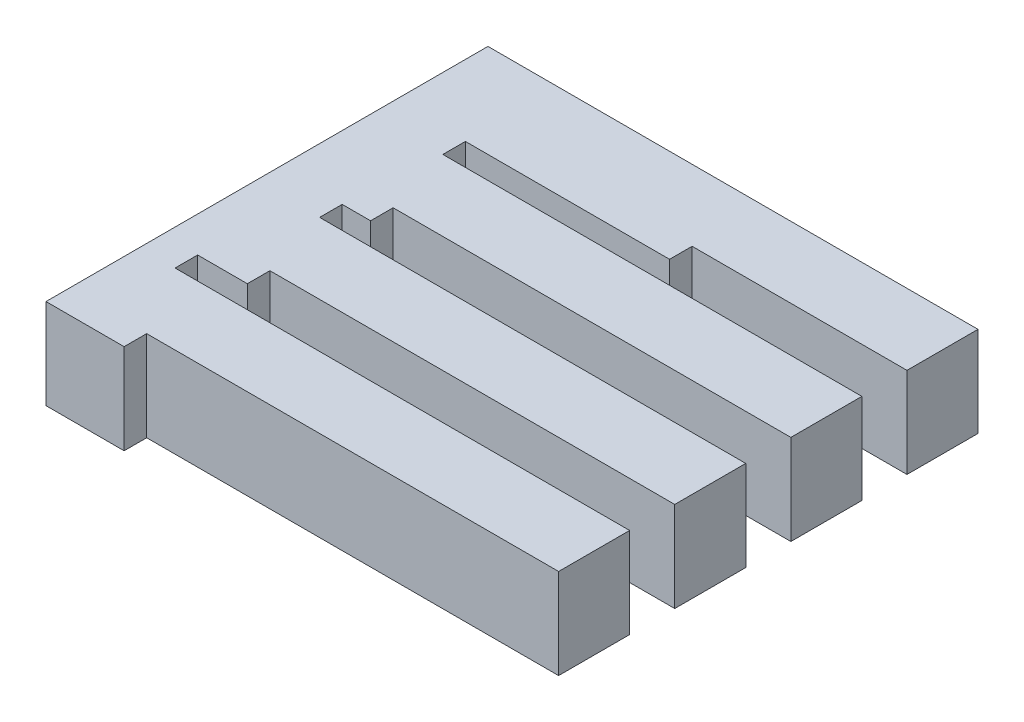
SolidWorks part; units mm, degrees
ref_plane "Front Plane" through (0, 0, 0) normal (0, 0, 1) x (1, 0, 0)
ref_plane "Top Plane" through (0, 0, 0) normal (0, 1, 0) x (1, 0, 0)
ref_plane "Right Plane" through (0, 0, 0) normal (1, 0, 0) x (0, 0, -1)
sketch "Sketch1" plane through (0, 0, 0) normal (0, 1, 0) x (1, 0, 0)
  line L0 (-34.5, -31.1125) -> (-23.5, -31.1125)
  line L1 (-23.5, -31.1125) -> (-23.5, -27.9375)
  line L2 (-23.5, -27.9375) -> (34.5, -27.9375)
  line L3 (34.5, -27.9375) -> (34.5, -17.9375)
  line L4 (34.5, -17.9375) -> (-29.5, -17.9375)
  line L5 (-29.5, -17.9375) -> (-29.5, -14.7625)
  line L6 (-29.5, -14.7625) -> (-22.5, -14.7625)
  line L7 (-22.5, -14.7625) -> (-22.5, -11.5875)
  line L8 (-22.5, -11.5875) -> (34.5, -11.5875)
  line L9 (34.5, -11.5875) -> (34.5, -1.5875)
  line L10 (34.5, -1.5875) -> (-25.5, -1.5875)
  line L11 (-25.5, -1.5875) -> (-25.5, 1.5875)
  line L12 (-25.5, 1.5875) -> (-21.5, 1.5875)
  line L13 (-21.5, 1.5875) -> (-21.5, 4.7625)
  line L14 (-21.5, 4.7625) -> (34.5, 4.7625)
  line L15 (34.5, 4.7625) -> (34.5, 14.7625)
  line L16 (34.5, 14.7625) -> (-24.5, 14.7625)
  line L17 (-24.5, 14.7625) -> (-24.5, 17.9375)
  line L18 (-24.5, 17.9375) -> (4.2457, 17.9375)
  line L19 (4.2457, 17.9375) -> (4.2457, 21.1125)
  line L20 (4.2457, 21.1125) -> (34.5, 21.1125)
  line L21 (34.5, 21.1125) -> (34.5, 31.1125)
  line L24 (34.5, 31.1125) -> (-34.5, 31.1125)
  line L25 (-34.5, 31.1125) -> (-34.5, -31.1125)
  point P22 (-34.5, 0)
  point P23 (0, 0)
  point P27 (0, 31.1125)
  dimension "D1" = 30.2543
  dimension "D2" = 56
  dimension "D3" = 57
  dimension "D4" = 58
  dimension "D5" = 59
  dimension "D6" = 60
  dimension "D7" = 64
  dimension "D8" = 3.175
  dimension "D9" = 10
  dimension "D10" = 5
extrude "Boss-Extrude1" add sketch "Sketch1" along normal mid plane 12.7
